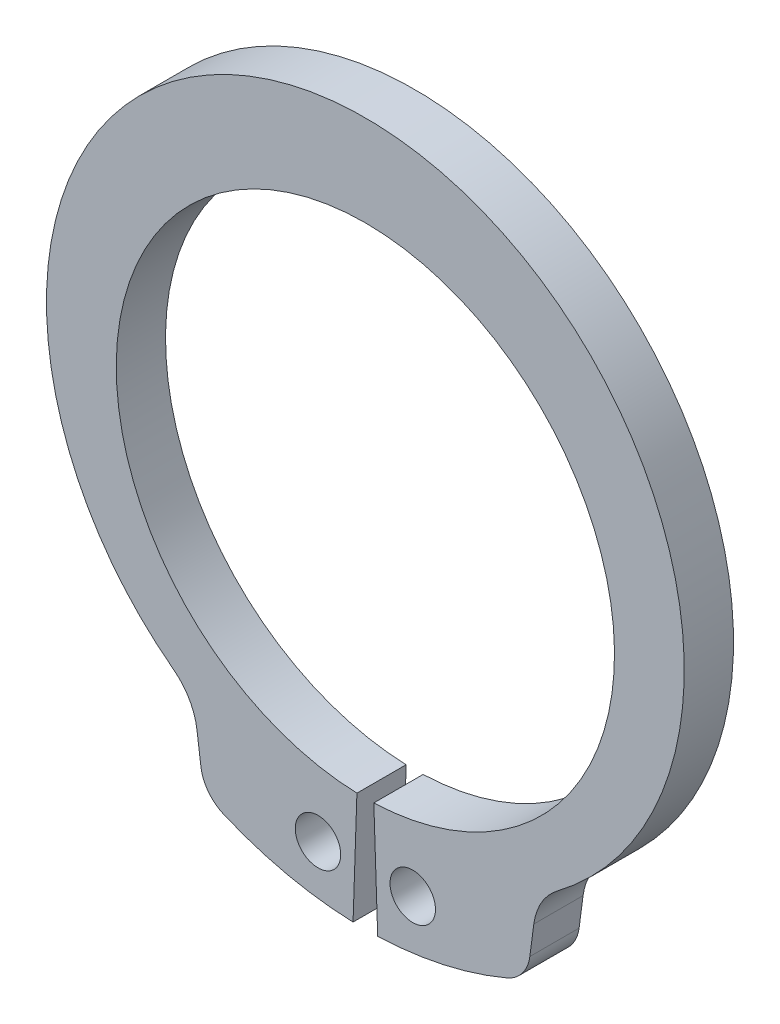
SolidWorks part; units mm, degrees
ref_plane "Plane1" through (0, 0, 0) normal (0, 0, 1) x (1, 0, 0)
ref_plane "Plane2" through (0, 0, 0) normal (0, 1, 0) x (1, 0, 0)
ref_plane "Plane3" through (0, 0, 0) normal (1, 0, 0) x (0, 0, -1)
sketch "Clipboard" plane through (0, 0, 0) normal (0, 0, 1) x (1, 0, 0)
  line L0 (0, 0) -> (2.4, 0)
  line L1 (0, 0) -> (0, 1.4)
  line L2 (0, 0) -> (0, -3)
  circle A0 centre (0, 0) radius 0.6
  circle A1 centre (0, 0) radius 7
  dimension "HoleDia" = 1.2
  dimension "ShaftDia" = 14
  dimension "LargeSection" = 2.4
  dimension "SmallSection" = 1.4
  dimension "LugSection" = 3
sketch "BodySke" plane through (0, 0, 0) normal (0, 0, 1) x (1, 0, 0)
  line L0 (-1.5431, 0) -> (1.5431, 0) construction
  line L1 (0, 0) -> (0, 8.975) construction
  line L2 (0.2232, -6.5712) -> (0.325, -9.5695)
  line L3 (-0.2232, -6.5712) -> (-0.325, -9.5695)
  line L4 (0, 0) -> (6.0306, -7.4372) construction
  line L5 (0, 0) -> (-6.0306, -7.4372) construction
  line L7 (4.4455, -7.2285) -> (4.3407, -8.0244)
  line L8 (-4.4455, -7.2285) -> (-4.3407, -8.0244)
  circle A0 centre (0, 0) radius 6.575 construction
  arc A1 (0.2232, -6.5712) -> (-0.2232, -6.5712) centre (0, 0) ccw
  arc A2 (5.0229, -6.1945) -> (-5.0229, -6.1945) centre (0, 0.5587) ccw construction
  arc A3 (0.325, -9.5695) -> (3.7398, -8.8144) centre (0, 0) ccw
  arc A4 (5.0679, -6.1608) -> (4.4455, -7.2285) centre (6.0306, -7.4372) ccw
  arc A5 (-4.4455, -7.2285) -> (-5.0679, -6.1608) centre (-6.0306, -7.4372) ccw
  arc A6 (-3.7398, -8.8144) -> (-0.325, -9.5695) centre (0, 0) ccw
  arc A7 (5.0679, -6.1608) -> (-5.0679, -6.1608) centre (0, 0.5587) ccw
  arc A8 (-4.4791, -6.9728) -> (4.4791, -6.9728) centre (0, 0) ccw construction
  circle A9 centre (1.25, -8.1927) radius 0.6
  circle A10 centre (-1.25, -8.1927) radius 0.6
  arc A11 (4.3407, -8.0244) -> (3.7398, -8.8144) centre (3.3492, -7.8939) cw
  arc A12 (-4.3407, -8.0244) -> (-3.7398, -8.8144) centre (-3.3492, -7.8939) ccw
  point P28 (4.2688, -8.5708)
  point P31 (-4.2688, -8.5708)
  dimension "GrooveDia" = 13.15
  dimension "D3" = 1
  dimension "LugRad" = 9.575
  dimension "HoleOffsetRad" = 8.2875
  dimension "HoleDia" = 1.2
  dimension "D2" = 15
  dimension "LargeRad" = 8.975
  dimension "SmallRad" = 7.975
  dimension "Gap" = 0.65
  dimension "SmallAngle" = 78.075
  dimension "HoleSpacing" = 2.5
extrude "Body" add sketch "BodySke" against normal blind 1.3
sketch "NotSke" plane through (0, 0, 0) normal (0, 0, 1) x (1, 0, 0)
  line L0 (1.25, -7.5927) -> (1.25, -8.7927)
  line L1 (1.25, -8.7927) -> (-1.25, -8.7927)
  line L2 (-1.25, -8.7927) -> (-1.25, -7.5927)
  line L3 (-1.25, -7.5927) -> (1.25, -7.5927)
  circle A0 centre (1.25, -8.1927) radius 0.6 construction
  circle A1 centre (-1.25, -8.1927) radius 0.6 construction
extrude "Notch" [suppressed] cut sketch "NotSke" against normal through all
equation "' \"ShaftDia@Clipboard\" = 10"
equation "' \"Thickness@Body\" = 0.9"
equation "' \"GrooveDia@BodySke\" = 9.4"
equation "' \"LugSection@Clipboard\" = 2.6"
equation "' \"LargeSection@Clipboard\" = 1.7"
equation "' \"SmallSection@Clipboard\" = 1.0"
equation "' \"HoleDia@Clipboard\" = 1.0"
equation "' \"ShaftDia@Clipboard\" = 30"
equation "' \"Thickness@Body\" = 2.4"
equation "' \"GrooveDia@BodySke\" = 28.2"
equation "' \"LugSection@Clipboard\" = 5.6"
equation "' \"LargeSection@Clipboard\" = 4.5"
equation "' \"SmallSection@Clipboard\" = 2.5"
equation "' \"HoleDia@Clipboard\" = 2.3"
equation "\"Gap@BodySke\" =  \"Thickness@Body\" / 2"
equation "\"LargeRad@BodySke\" =  \"GrooveDia@BodySke\" / 2 +  \"LargeSection@Clipboard\""
equation "\"SmallRad@BodySke\" =  \"GrooveDia@BodySke\" / 2 +  \"SmallSection@Clipboard\""
equation "\"LugRad@BodySke\" = \"GrooveDia@BodySke\" / 2 + \"LugSection@Clipboard\""
equation "\"HoleOffsetRad@BodySke\" = (  \"ShaftDia@Clipboard\" / 2 + \"LugRad@BodySke\" ) / 2"
equation "\"HoleSpacing@BodySke\" = \"Gap@BodySke\"  * 2 +  \"HoleDia@Clipboard\""
equation "\"HoleDia@BodySke\" =  \"HoleDia@Clipboard\""
equation "\"SmallAngle@BodySke\" = atn(\"HoleSpacing@BodySke\" / 2 / sqr(\"HoleOffsetRad@BodySke\"  * \"HoleOffsetRad@BodySke\" - (\"HoleSpacing@BodySke\" / 2) * (\"HoleSpacing@BodySke\" / 2) ))  * 9 * ( 180 / 3.141593)"
